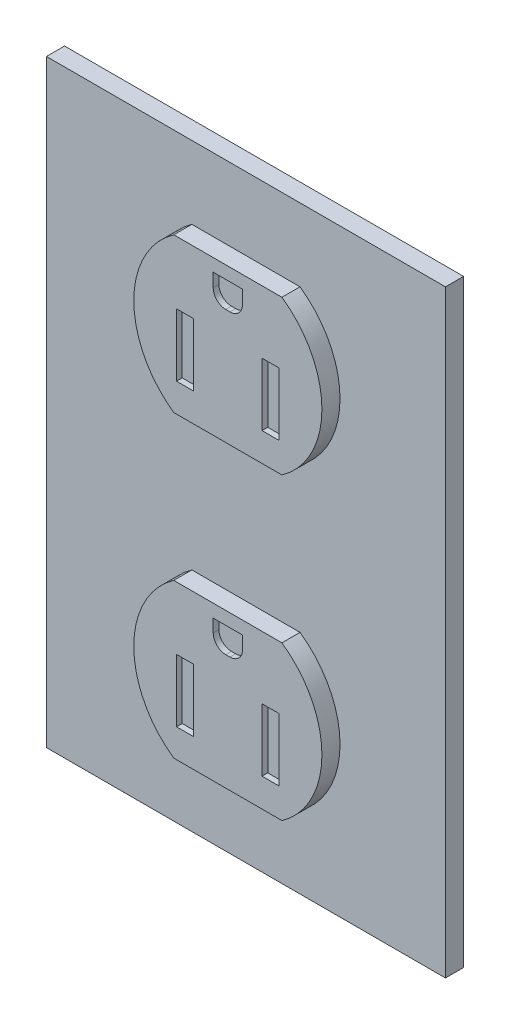
SolidWorks part; units mm, degrees
ref_plane "Alzado" through (0, 0, 0) normal (0, 0, 1) x (1, 0, 0)
ref_plane "Planta" through (0, 0, 0) normal (0, 1, 0) x (1, 0, 0)
ref_plane "Vista lateral" through (0, 0, 0) normal (1, 0, 0) x (0, 0, -1)
sketch "Croquis1" plane through (0, 0, 0) normal (0, 0, 1) x (1, 0, 0)
  line L1 (0, 0) -> (70, 0)
  line L2 (0, 0) -> (0, -105)
  line L3 (0, -105) -> (70, -105)
  line L4 (70, 0) -> (70, -105)
  dimension "D1" = 70
  dimension "D2" = 105
extrude "Saliente-Extruir1" add sketch "Croquis1" along normal blind 3.175
sketch "Croquis2" plane through (0, 0, 3.175) normal (0, 0, 1) x (1, 0, 0)
  line L0 (35, 0) -> (35, -52.5) construction
  line L1 (70, 0) -> (0, 0) construction
  line L2 (35, -52.5) -> (70, -52.5) construction
  line L3 (70, -105) -> (70, 0) construction
  circle A0 centre (35, -26.25) radius 16.5
  circle A1 centre (35, -78.75) radius 16.5
  dimension "D1" = 33
extrude "Saliente-Extruir2" add sketch "Croquis2" along normal blind 3.175
sketch "Croquis3" plane through (0, 0, 6.35) normal (0, 0, 1) x (1, 0, 0)
  line L0 (18.5, -26.25) -> (51.5, -26.25) construction
  line L1 (18.5, -78.75) -> (51.5, -78.75) construction
  line L2 (22, -45.75) -> (48, -39.75) construction
  line L3 (22, -12.75) -> (48, -12.75)
  line L4 (22, -12.75) -> (22, -6.75)
  line L5 (22, -6.75) -> (48, -6.75)
  line L6 (48, -12.75) -> (48, -6.75)
  line L7 (22, -12.75) -> (48, -6.75) construction
  line L8 (22, -6.75) -> (48, -12.75) construction
  line L9 (22, -39.75) -> (48, -45.75) construction
  line L10 (48, -39.75) -> (48, -45.75)
  line L11 (22, -45.75) -> (48, -45.75)
  line L12 (22, -39.75) -> (22, -45.75)
  line L13 (22, -39.75) -> (48, -39.75)
  line L14 (0, -52.5) -> (70, -52.5) construction
  line L15 (0, 0) -> (0, -105) construction
  line L16 (70, -105) -> (70, 0) construction
  line L17 (22, -65.25) -> (48, -59.25) construction
  line L18 (22, -98.25) -> (48, -92.25) construction
  line L19 (22, -92.25) -> (48, -98.25) construction
  line L20 (22, -59.25) -> (48, -65.25) construction
  line L21 (18.5, -78.75) -> (51.5, -78.75) construction
  line L22 (22, -65.25) -> (48, -65.25)
  line L23 (22, -65.25) -> (22, -59.25)
  line L24 (22, -59.25) -> (48, -59.25)
  line L25 (48, -65.25) -> (48, -59.25)
  line L26 (48, -92.25) -> (48, -98.25)
  line L27 (22, -98.25) -> (48, -98.25)
  line L28 (22, -92.25) -> (22, -98.25)
  line L29 (22, -92.25) -> (48, -92.25)
  circle A0 centre (35, -26.25) radius 16.5 construction
  circle A1 centre (35, -26.25) radius 16.5 construction
  circle A2 centre (35, -78.75) radius 16.5 construction
  circle A3 centre (35, -78.75) radius 16.5 construction
  point P14 (35, -9.75)
  point P23 (35, -42.75)
  point P38 (35, -62.25)
  point P39 (35, -95.25)
  dimension "D1" = 6
  dimension "D2" = 26
extrude "Cortar-Extruir1" cut sketch "Croquis3" against normal up to surface (3.175 mm away) up to face at (18.5, -78.75, 3.175)
sketch "Croquis4" plane through (0, 0, 6.35) normal (0, 0, 1) x (1, 0, 0)
  line L0 (19.1255, -21.75) -> (50.8745, -21.75) construction
  line L1 (35, -21.75) -> (35, -39.75) construction
  line L2 (25.5132, -39.75) -> (44.4868, -39.75) construction
  line L3 (25.5132, -12.75) -> (44.4868, -12.75) construction
  line L4 (26, -34.75) -> (29, -34.75)
  line L5 (26, -34.75) -> (26, -23.75)
  line L6 (26, -23.75) -> (29, -23.75)
  line L7 (29, -34.75) -> (29, -23.75)
  line L8 (26, -34.75) -> (29, -23.75) construction
  line L9 (26, -23.75) -> (29, -34.75) construction
  line L10 (44, -23.75) -> (41, -34.75) construction
  line L11 (44, -34.75) -> (41, -23.75) construction
  line L12 (41, -34.75) -> (41, -23.75)
  line L13 (44, -23.75) -> (41, -23.75)
  line L14 (44, -34.75) -> (44, -23.75)
  line L15 (44, -34.75) -> (41, -34.75)
  line L16 (35, -21.75) -> (35, -12.75) construction
  line L17 (35, -74.25) -> (35, -92.25) construction
  line L18 (34.6321, -19.5329) -> (35.3679, -19.5329)
  line L19 (32.4321, -17.3329) -> (32.4321, -14.9671)
  line L20 (32.4321, -14.9671) -> (37.5679, -14.9671)
  line L21 (37.5679, -17.3329) -> (37.5679, -14.9671)
  line L22 (32.4321, -19.5329) -> (37.5679, -14.9671) construction
  line L23 (32.4321, -14.9671) -> (37.5679, -19.5329) construction
  line L25 (25.5132, -92.25) -> (44.4868, -92.25) construction
  line L26 (19.1255, -74.25) -> (50.8745, -74.25) construction
  line L27 (44.4868, -65.25) -> (25.5132, -65.25) construction
  line L28 (41, -76.25) -> (41, -87.25)
  line L29 (26, -76.25) -> (29, -76.25)
  line L30 (26, -76.25) -> (26, -87.25)
  line L31 (26, -87.25) -> (29, -87.25)
  line L32 (29, -76.25) -> (29, -87.25)
  line L33 (44, -87.25) -> (41, -87.25)
  line L34 (44, -76.25) -> (44, -87.25)
  line L35 (44, -76.25) -> (41, -76.25)
  line L36 (35, -74.25) -> (35, -65.25) construction
  line L38 (34.6321, -71.9736) -> (35.3679, -71.9736)
  line L39 (32.4321, -69.7736) -> (32.4321, -67.5264)
  line L40 (32.4321, -67.5264) -> (37.5679, -67.5264)
  line L41 (37.5679, -69.7736) -> (37.5679, -67.5264)
  line L42 (32.4321, -71.9736) -> (37.5679, -67.5264) construction
  line L43 (32.4321, -67.5264) -> (37.5679, -71.9736) construction
  arc A0 (25.5132, -12.75) -> (25.5132, -39.75) centre (35, -26.25) ccw construction
  arc A1 (44.4868, -39.75) -> (44.4868, -12.75) centre (35, -26.25) ccw construction
  arc A2 (35.3679, -19.5329) -> (37.5679, -17.3329) centre (35.3679, -17.3329) ccw
  arc A3 (34.6321, -19.5329) -> (32.4321, -17.3329) centre (34.6321, -17.3329) cw
  arc A4 (25.5132, -65.25) -> (25.5132, -92.25) centre (35, -78.75) ccw construction
  arc A5 (44.4868, -92.25) -> (44.4868, -65.25) centre (35, -78.75) ccw construction
  arc A6 (35.3679, -71.9736) -> (37.5679, -69.7736) centre (35.3679, -69.7736) ccw
  arc A7 (34.6321, -71.9736) -> (32.4321, -69.7736) centre (34.6321, -69.7736) cw
  point P12 (27.5, -29.25)
  point P23 (42.5, -29.25)
  point P24 (35, -17.25)
  point P36 (35, -69.75)
  dimension "D6" = 2.2
  dimension "D12" = 2.2
  dimension "D1" = 11
  dimension "D2" = 3
  dimension "D3" = 6
  dimension "D4" = 4
  dimension "D5" = 9
  dimension "D7" = 9
  dimension "D8" = 2
  dimension "D9" = 6
  dimension "D10" = 11
  dimension "D11" = 3
extrude "Cortar-Extruir2" cut sketch "Croquis4" against normal blind 1
